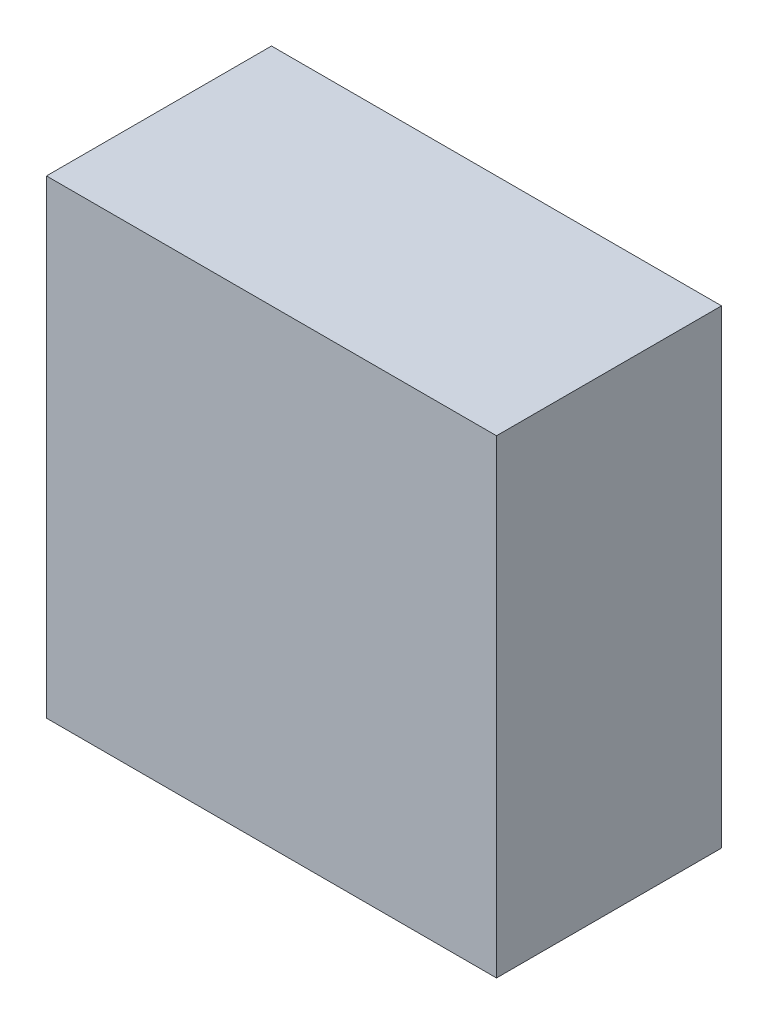
SolidWorks part; units mm, degrees
ref_plane "Front Plane" through (0, 0, 0) normal (0, 0, 1) x (1, 0, 0)
ref_plane "Top Plane" through (0, 0, 0) normal (0, 1, 0) x (1, 0, 0)
ref_plane "Right Plane" through (0, 0, 0) normal (1, 0, 0) x (0, 0, -1)
sketch "Sketch1" plane through (0, 0, 0) normal (0, 1, 0) x (1, 0, 0)
  line L1 (0, 0) -> (23, 0)
  line L2 (0, 0) -> (0, 11.5)
  line L3 (0, 11.5) -> (23, 11.5)
  line L4 (23, 0) -> (23, 11.5)
  dimension "D1" = 11.5
  dimension "D2" = 23
extrude "Boss-Extrude1" add sketch "Sketch1" along normal blind 24
